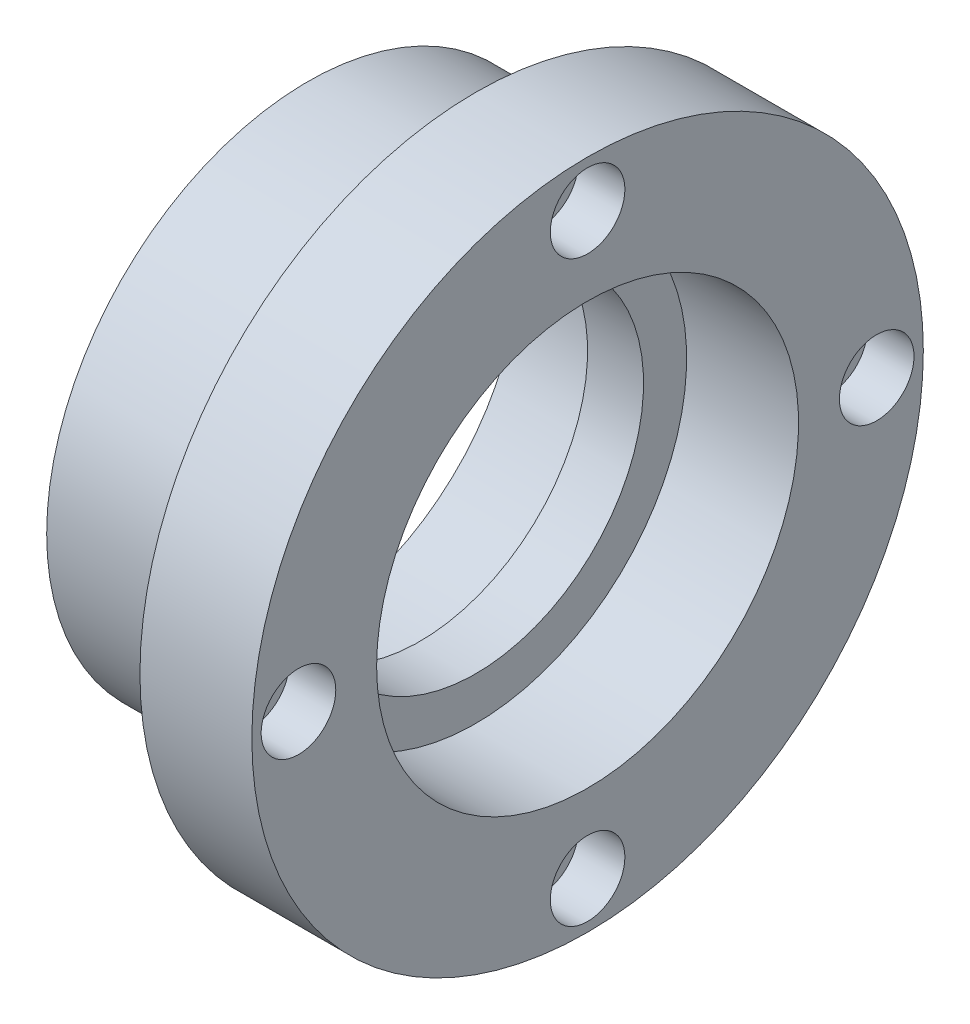
SolidWorks part; units mm, degrees
ref_plane "Front" through (0, 0, 0) normal (0, 0, 1) x (1, 0, 0)
ref_plane "Top" through (0, 0, 0) normal (0, 1, 0) x (1, 0, 0)
ref_plane "Right" through (0, 0, 0) normal (1, 0, 0) x (0, 0, -1)
sketch "Sketch1" plane through (0, 0, 0) normal (0, 0, 1) x (1, 0, 0)
  line L0 (-59.7297, 0) -> (49.8078, 0) construction
  line L1 (-30, 22.6219) -> (-18, 22.6219)
  line L2 (-18, 22.6219) -> (-18, 18)
  line L3 (-18, 18) -> (-12, 18)
  line L4 (-12, 18) -> (-12, 22.6219)
  line L5 (-12, 22.6219) -> (0, 22.6219)
  line L6 (0, 22.6219) -> (0, 36)
  line L7 (0, 36) -> (-12, 36)
  line L8 (-30, 28) -> (-30, 22.6219)
  line L9 (-12, 36) -> (-12, 28)
  line L10 (-12, 28) -> (-30, 28)
  dimension "D1" = 45.2437
  dimension "D2" = 45.2437
  dimension "D3" = 36
  dimension "D4" = 12
  dimension "D5" = 12
  dimension "D6" = 8
  dimension "D7" = 72
  dimension "D8" = 6
revolve "Revolve1" add sketch "Sketch1" angle 360 about L0
hole_wizard "CBORE for M4 SHCS1" positions "Sketch3" profile "Sketch2" counterbore size "M4" standard "ANSI Metric" end condition through all
sketch "Sketch3" plane through (0, 0, 0) normal (1, 0, 0) x (0, 0, -1)
  point P0 (0, 31)
  dimension "D1" = 31
sketch "Sketch2" plane through (0, 31, 0) normal (0, 1, 0) x (0, 0, -1)
  line L0 (0, 0) -> (0, 30)
  line L1 (0, 30) -> (2.25, 30)
  line L3 (2.25, 30) -> (2.25, 5)
  line L4 (2.25, 5) -> (4, 5)
  line L5 (4, 5) -> (4, 0)
  line L7 (4, 0) -> (0, 0)
  line L11 (0, -6.35) -> (0, 107.95) construction
  dimension "Thru Hole Dia." = 4.5
  dimension "Thru Hole Depth" = 30
  dimension "C'Bore Dia." = 8
  dimension "C'Bore Depth" = 5
pattern_circular "CirPattern1" count 4 over 360 about axis through (0, 0, 0) along (1, 0, 0) of "CBORE for M4 SHCS1"
